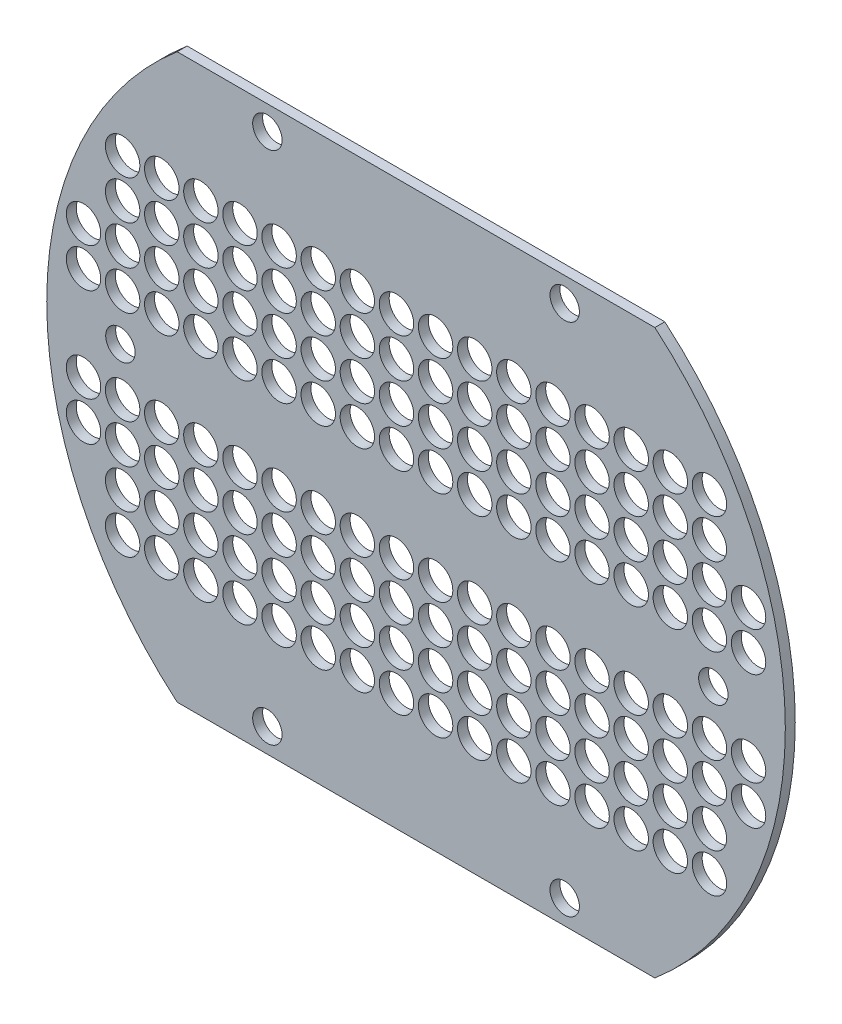
SolidWorks part; units mm, degrees
ref_plane "Front Plane" through (0, 0, 0) normal (0, 0, 1) x (1, 0, 0)
ref_plane "Top Plane" through (0, 0, 0) normal (0, 1, 0) x (1, 0, 0)
ref_plane "Right Plane" through (0, 0, 0) normal (1, 0, 0) x (0, 0, -1)
sketch "Sketch1" plane through (0, 0, 0) normal (0, 0, 1) x (1, 0, 0)
  line L0 (-233.9819, -24.0828) -> (238.0181, -24.0828) construction
  line L1 (-150.6121, 155.9172) -> (154.6484, 155.9172)
  line L2 (-150.6121, -204.0828) -> (154.6484, -204.0828)
  arc A0 (237.1141, -3.4461) -> (154.6484, 155.9172) centre (2.0181, -24.0828) ccw
  circle A1 centre (-210.4819, -79.0828) radius 11
  circle A2 centre (-185.4819, -79.0828) radius 11
  circle A3 centre (-135.4819, -79.0828) radius 11
  circle A4 centre (-110.4819, -79.0828) radius 11
  circle A5 centre (-85.4819, -79.0828) radius 11
  circle A6 centre (-60.4819, -79.0828) radius 11
  circle A7 centre (-35.4819, -79.0828) radius 11
  circle A8 centre (-10.4819, -79.0828) radius 11
  circle A9 centre (214.5181, -79.0828) radius 11
  circle A10 centre (214.5181, -54.0828) radius 11
  circle A11 centre (189.5181, -79.0828) radius 11
  circle A12 centre (189.5181, -54.0828) radius 11
  circle A13 centre (164.5181, -54.0828) radius 11
  circle A14 centre (164.5181, -79.0828) radius 11
  circle A15 centre (139.5181, -79.0828) radius 11
  circle A16 centre (139.5181, -54.0828) radius 11
  circle A17 centre (114.5181, -54.0828) radius 11
  circle A18 centre (114.5181, -79.0828) radius 11
  circle A19 centre (89.5181, -79.0828) radius 11
  circle A20 centre (89.5181, -54.0828) radius 11
  circle A21 centre (64.5181, -79.0828) radius 11
  circle A22 centre (64.5181, -54.0828) radius 11
  circle A23 centre (39.5181, -79.0828) radius 11
  circle A24 centre (39.5181, -54.0828) radius 11
  circle A25 centre (14.5181, -54.0828) radius 11
  circle A26 centre (-10.4819, -54.0828) radius 11
  circle A27 centre (-35.4819, -54.0828) radius 11
  circle A28 centre (-60.4819, -54.0828) radius 11
  circle A29 centre (-85.4819, -54.0828) radius 11
  circle A30 centre (-110.4819, -54.0828) radius 11
  circle A31 centre (-135.4819, -54.0828) radius 11
  circle A32 centre (-160.4819, -54.0828) radius 11
  circle A33 centre (-185.4819, -54.0828) radius 11
  circle A34 centre (-210.4819, -54.0828) radius 11
  circle A35 centre (97.0181, 140.462) radius 9.398
  circle A36 centre (-92.9819, 140.462) radius 9.398
  circle A37 centre (-60.4819, 5.9172) radius 11
  circle A38 centre (-35.4819, 5.9172) radius 11
  circle A39 centre (-35.4819, 30.9172) radius 11
  circle A40 centre (-60.4819, 30.9172) radius 11
  circle A41 centre (-60.4819, 55.9172) radius 11
  circle A42 centre (-35.4819, 55.9172) radius 11
  circle A43 centre (-10.4819, 55.9172) radius 11
  circle A44 centre (-10.4819, 30.9172) radius 11
  circle A45 centre (-10.4819, 5.9172) radius 11
  circle A46 centre (14.5181, 5.9172) radius 11
  circle A47 centre (14.5181, 30.9172) radius 11
  circle A48 centre (14.5181, 55.9172) radius 11
  circle A49 centre (39.5181, 55.9172) radius 11
  circle A50 centre (39.5181, 30.9172) radius 11
  circle A51 centre (39.5181, 5.9172) radius 11
  circle A52 centre (64.5181, 5.9172) radius 11
  circle A53 centre (64.5181, 55.9172) radius 11
  circle A54 centre (64.5181, 30.9172) radius 11
  circle A55 centre (89.5181, 30.9172) radius 11
  circle A56 centre (89.5181, 5.9172) radius 11
  circle A57 centre (89.5181, 55.9172) radius 11
  circle A58 centre (114.5181, 55.9172) radius 11
  circle A59 centre (114.5181, 30.9172) radius 11
  circle A60 centre (114.5181, 5.9172) radius 11
  circle A61 centre (139.5181, 5.9172) radius 11
  circle A62 centre (139.5181, 30.9172) radius 11
  circle A63 centre (139.5181, 55.9172) radius 11
  circle A64 centre (164.5181, 55.9172) radius 11
  circle A65 centre (164.5181, 30.9172) radius 11
  circle A66 centre (164.5181, 5.9172) radius 11
  circle A67 centre (189.5181, 5.9172) radius 11
  circle A68 centre (214.5181, 5.9172) radius 11
  circle A69 centre (214.5181, 30.9172) radius 11
  circle A70 centre (189.5181, 30.9172) radius 11
  circle A71 centre (189.5181, 55.9172) radius 11
  circle A72 centre (189.5181, 80.9172) radius 11
  circle A73 centre (164.5181, 80.9172) radius 11
  circle A74 centre (139.5181, 80.9172) radius 11
  circle A75 centre (114.5181, 80.9172) radius 11
  circle A76 centre (89.5181, 80.9172) radius 11
  circle A77 centre (64.5181, 80.9172) radius 11
  circle A78 centre (39.5181, 80.9172) radius 11
  circle A79 centre (14.5181, 80.9172) radius 11
  circle A80 centre (-10.4819, 80.9172) radius 11
  circle A81 centre (-35.4819, 80.9172) radius 11
  circle A82 centre (-60.4819, 80.9172) radius 11
  circle A83 centre (-85.4819, 80.9172) radius 11
  circle A84 centre (-85.4819, 55.9172) radius 11
  circle A85 centre (-85.4819, 30.9172) radius 11
  circle A86 centre (-85.4819, 5.9172) radius 11
  circle A87 centre (-110.4819, 5.9172) radius 11
  circle A88 centre (-110.4819, 30.9172) radius 11
  circle A89 centre (-110.4819, 55.9172) radius 11
  circle A90 centre (-110.4819, 80.9172) radius 11
  circle A91 centre (-135.4819, 80.9172) radius 11
  circle A92 centre (-135.4819, 55.9172) radius 11
  circle A93 centre (-135.4819, 30.9172) radius 11
  circle A94 centre (-135.4819, 5.9172) radius 11
  circle A95 centre (-160.4819, 5.9172) radius 11
  circle A96 centre (-160.4819, 30.9172) radius 11
  circle A97 centre (-160.4819, 80.9172) radius 11
  circle A98 centre (-185.4819, 55.9172) radius 11
  circle A99 centre (-160.4819, 55.9172) radius 11
  circle A100 centre (-185.4819, 80.9172) radius 11
  circle A101 centre (-185.4819, 30.9172) radius 11
  circle A102 centre (-185.4819, 5.9172) radius 11
  circle A103 centre (-210.4819, 5.9172) radius 11
  circle A104 centre (-210.4819, 30.9172) radius 11
  arc A105 (-233.0779, -44.7196) -> (-223.3616, -94.0826) centre (2.0181, -24.0828) ccw
  arc A106 (227.3979, -94.0826) -> (154.6484, 155.9172) centre (2.0181, -24.0828) ccw
  circle A107 centre (-160.4819, -79.0828) radius 11
  circle A108 centre (14.5181, -79.0828) radius 11
  arc A109 (227.3979, -94.0826) -> (237.1141, -44.7196) centre (2.0181, -24.0828) ccw
  circle A110 centre (2.5588, -23.1366) radius 189.4532 construction
  circle A111 centre (-186.892, -24.0828) radius 9.398
  circle A112 centre (192.0097, -24.0828) radius 9.398
  arc A113 (237.1141, -44.7196) -> (154.6484, -204.0828) centre (2.0181, -24.0828) cw
  circle A114 centre (2.5588, -25.0291) radius 189.4532 construction
  arc A115 (227.3979, 45.9169) -> (154.6484, -204.0828) centre (2.0181, -24.0828) cw
  circle A116 centre (-185.4819, -129.0828) radius 11
  circle A117 centre (-160.4819, -104.0828) radius 11
  circle A118 centre (-185.4819, -104.0828) radius 11
  circle A119 centre (-160.4819, -129.0828) radius 11
  circle A120 centre (-135.4819, -104.0828) radius 11
  circle A121 centre (-135.4819, -129.0828) radius 11
  circle A122 centre (-110.4819, -129.0828) radius 11
  circle A123 centre (-110.4819, -104.0828) radius 11
  circle A124 centre (-85.4819, -104.0828) radius 11
  circle A125 centre (-85.4819, -129.0828) radius 11
  circle A126 centre (-60.4819, -129.0828) radius 11
  circle A127 centre (-35.4819, -129.0828) radius 11
  circle A128 centre (-10.4819, -129.0828) radius 11
  circle A129 centre (14.5181, -129.0828) radius 11
  circle A130 centre (39.5181, -129.0828) radius 11
  circle A131 centre (64.5181, -129.0828) radius 11
  circle A132 centre (89.5181, -129.0828) radius 11
  circle A133 centre (114.5181, -129.0828) radius 11
  circle A134 centre (139.5181, -129.0828) radius 11
  circle A135 centre (164.5181, -129.0828) radius 11
  circle A136 centre (189.5181, -129.0828) radius 11
  circle A137 centre (189.5181, -104.0828) radius 11
  circle A138 centre (164.5181, -104.0828) radius 11
  circle A139 centre (139.5181, -104.0828) radius 11
  circle A140 centre (114.5181, -104.0828) radius 11
  circle A141 centre (89.5181, -104.0828) radius 11
  circle A142 centre (64.5181, -104.0828) radius 11
  circle A143 centre (39.5181, -104.0828) radius 11
  circle A144 centre (14.5181, -104.0828) radius 11
  circle A145 centre (-10.4819, -104.0828) radius 11
  circle A146 centre (-35.4819, -104.0828) radius 11
  circle A147 centre (-60.4819, -104.0828) radius 11
  circle A148 centre (-92.9819, -188.6277) radius 9.398
  circle A149 centre (97.0181, -188.6277) radius 9.398
  arc A150 (-150.6121, 155.9172) -> (-233.0779, -3.4461) centre (2.0181, -24.0828) ccw
  arc A151 (-150.6121, 155.9172) -> (-223.3616, -94.0826) centre (2.0181, -24.0828) ccw
  arc A152 (-150.6121, -204.0828) -> (-233.0779, -44.7196) centre (2.0181, -24.0828) cw
  arc A153 (-150.6121, -204.0828) -> (-223.3616, 45.9169) centre (2.0181, -24.0828) cw
extrude "Boss-Extrude1" add sketch "Sketch1" along normal mid plane 6.35 contours A152 L2 A113 A106 A0 L1 A150 A151 A105 A148 A146 A144 A142 A140 A138 A136 A134 A132 A130 A128 A126 A124 A122 A120 A118 A116 A112 A111
